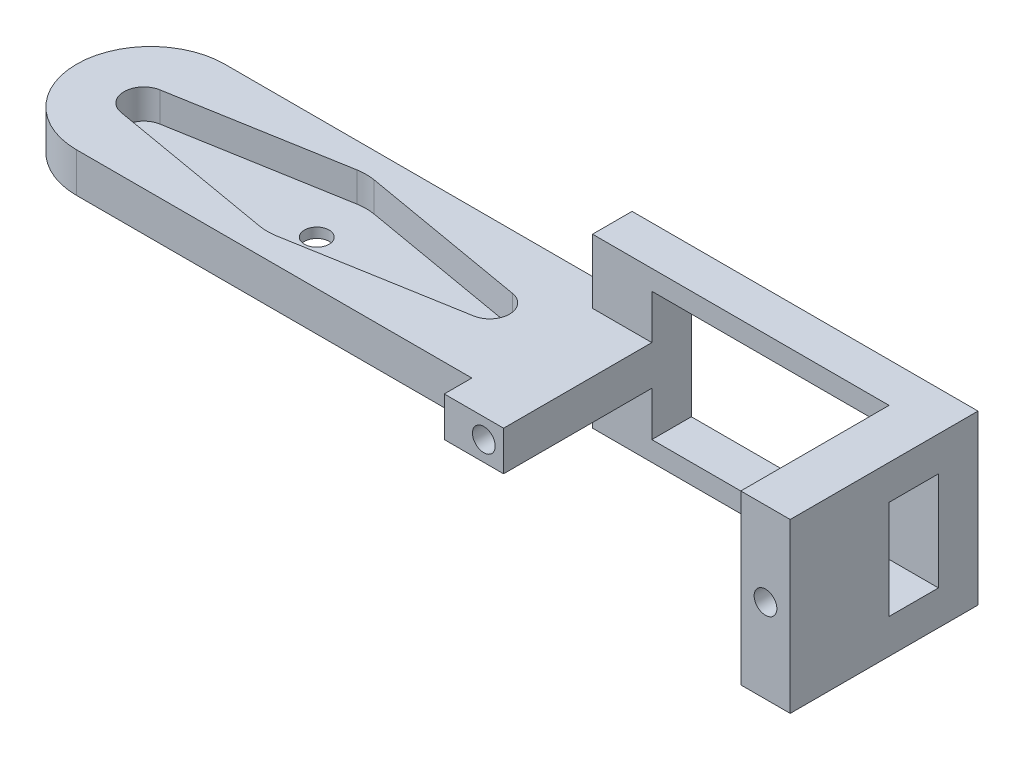
SolidWorks part; units mm, degrees
ref_plane "前基準面" through (0, 0, 0) normal (0, 0, 1) x (1, 0, 0)
ref_plane "上基準面" through (0, 0, 0) normal (0, 1, 0) x (1, 0, 0)
ref_plane "右基準面" through (0, 0, 0) normal (1, 0, 0) x (0, 0, -1)
sketch "草圖1" plane through (0, 0, 0) normal (0, 0, 1) x (1, 0, 0)
  line L0 (-21.2211, 2.8) -> (13.7789, 2.8) construction
  line L1 (-21.2211, 11.3) -> (13.7789, 11.3)
  line L2 (-21.2211, 11.3) -> (-21.2211, -5.7)
  line L3 (-21.2211, -5.7) -> (13.7789, -5.7)
  line L4 (13.7789, 11.3) -> (13.7789, -5.7)
  dimension "D1" = 35
  dimension "D2" = 8.5
extrude "填料-伸長1" add sketch "草圖1" along normal blind 4
sketch "草圖2" plane through (0, 0, 0) normal (0, 0, 1) x (1, 0, 0)
  line L0 (-21.2211, 2.8) -> (13.7789, 2.8) construction
  line L1 (-21.2211, 11.3) -> (-21.2211, -5.7) construction
  line L2 (13.7789, -5.7) -> (13.7789, 11.3) construction
  line L3 (-3.7211, 11.3) -> (-3.7211, -5.7) construction
  line L4 (13.7789, 11.3) -> (-21.2211, 11.3) construction
  line L5 (-21.2211, -5.7) -> (13.7789, -5.7) construction
  line L7 (-15.2211, 9.3) -> (8.7789, 9.3)
  line L8 (-15.2211, 9.3) -> (-15.2211, -3.7)
  line L9 (-15.2211, -3.7) -> (8.7789, -3.7)
  line L10 (8.7789, 9.3) -> (8.7789, -3.7)
  dimension "D1" = 24
  dimension "D2" = 13
  dimension "D3" = 6.5
  dimension "D4" = 5
extrude "除料-伸長1" cut sketch "草圖2" along normal blind 6
ref_plane "平面1" through (13.7789, 0, 0) normal (1, 0, 0) x (0, 0, -1)
sketch "草圖3" plane through (13.7789, 0, 0) normal (1, 0, 0) x (0, 0, -1)
  line L0 (-4, 2.8025) -> (-19, 2.8025) construction
  line L1 (-4, 11.3) -> (-19, 11.3)
  line L3 (-4, -5.6949) -> (-19, -5.6949)
  line L4 (-19, 11.3) -> (-19, -5.6949)
  line L5 (-4, 11.3) -> (-4, -5.6949)
  line L6 (-9, 7.8025) -> (-4, 7.8025)
  line L7 (-9, 7.8025) -> (-9, -2.1975)
  line L8 (-9, -2.1975) -> (-4, -2.1975)
  line L9 (-4, 7.8025) -> (-4, -2.1975)
  dimension "D1" = 15
  dimension "D2" = 5
  dimension "D3" = 10
  dimension "D4" = 5
extrude "填料-伸長2" add sketch "草圖3" against normal blind 5 contours L7 L0 L4 L3 L5 L8 | L0 L7 L6 L5 L1 L4
ref_plane "平面2" through (0, 0, 4) normal (0, 0, 1) x (1, 0, 0)
sketch "草圖5" plane through (0, 0, 4) normal (0, 0, 1) x (1, 0, 0)
  line L0 (-21.2211, 2.8) -> (-15.2211, 2.8) construction
  line L1 (-21.2211, 11.3) -> (-21.2211, -5.7) construction
  line L2 (-15.2211, -3.7) -> (-15.2211, 9.3) construction
  line L3 (-17.2211, 4.8) -> (-17.2211, 0.8) construction
  line L4 (-19.2211, 4.8) -> (-15.2211, 4.8)
  line L5 (-19.2211, 4.8) -> (-19.2211, 0.8)
  line L6 (-19.2211, 0.8) -> (-15.2211, 0.8)
  line L7 (-15.2211, 4.8) -> (-15.2211, 0.8)
  circle A0 centre (-17.2211, 2.8) radius 1.15
  dimension "D4" = 2.3
  dimension "D1" = 4
  dimension "D2" = 4
  dimension "D3" = 2
extrude "填料-伸長3" add sketch "草圖5" along normal blind 15
ref_plane "平面3" through (0, 0, 19) normal (0, 0, 1) x (1, 0, 0)
sketch "草圖6" plane through (0, 0, 19) normal (0, 0, 1) x (1, 0, 0)
  line L0 (8.7789, 2.8025) -> (13.7789, 2.8025) construction
  line L1 (8.7789, 11.3) -> (8.7789, -5.6949) construction
  line L2 (13.7789, -9.35) -> (13.7789, 9.35) construction
  line L3 (11.2789, 11.3) -> (11.2789, -5.6949) construction
  line L4 (8.7789, 11.3) -> (13.7789, 11.3) construction
  line L5 (8.7789, -5.6949) -> (13.7789, -5.6949) construction
  circle A0 centre (11.2789, 2.8025) radius 1.15
  dimension "D1" = 2.3
extrude "除料-伸長2" cut sketch "草圖6" against normal blind 15
ref_plane "平面4" through (-21.2211, 0, 0) normal (-1, 0, 0) x (0, 0, 1)
sketch "草圖7" plane through (-21.2211, 0, 0) normal (-1, 0, 0) x (0, 0, 1)
  line L6 (4, 4.8) -> (4, 0.7965)
  line L7 (4, -9.35) -> (4, 9.35) construction
  line L8 (19, 4.8) -> (4, 4.8) construction
  line L9 (4, 0.7965) -> (19, 0.8)
  line L10 (19, -2.75) -> (19, 2.75) construction
  line L11 (19, 0.8) -> (4, 0.8) construction
  line L12 (19, 0.8) -> (19, 4.8)
  line L13 (19, 4.8) -> (4, 4.8)
extrude "填料-伸長5" add sketch "草圖7" against normal blind 2
ref_plane "平面5" through (0, 0.8, 0) normal (0, -1, 0) x (-1, 0, 0)
sketch "草圖9" plane through (0, 0.8, 0) normal (0, -1, 0) x (-1, 0, 0)
  line L0 (21.2211, -1.2098) -> (21.2211, -16.2098)
  line L1 (21.2211, -4) -> (21.2211, 0) construction
  line L2 (21.2211, -4) -> (21.2211, -19) construction
  line L3 (21.2211, -16.2098) -> (61.2211, -16.2098)
  line L4 (21.2211, -1.2098) -> (61.2211, -1.2098)
  arc A0 (61.2211, -1.2098) -> (61.2211, -16.2098) centre (61.2211, -8.7098) cw
  dimension "D1" = 15
  dimension "D2" = 40
  dimension "D3" = 40
extrude "填料-伸長6" add sketch "草圖9" against normal blind 4
ref_plane "平面6" through (0, 4.8, 0) normal (0, 1, 0) x (1, 0, 0)
sketch "草圖10" plane through (0, 4.8, 0) normal (0, 1, 0) x (1, 0, 0)
  line L4 (-68.7211, -8.7098) -> (-59.9107, -8.7098) construction
  line L5 (-45.2679, -3.7838) -> (-62.2536, -6.7394)
  line L6 (-44.4107, -13.7098) -> (-44.4107, -16.2098) construction
  line L7 (-21.2211, -16.2098) -> (-61.2211, -16.2098) construction
  line L8 (-45.2679, -13.6358) -> (-62.2536, -10.6802)
  line L9 (-43.5536, -13.6358) -> (-26.5679, -10.6802)
  line L10 (-43.5536, -3.7838) -> (-26.5679, -6.7394)
  line L11 (-24.9107, -8.7098) -> (-20.1004, -8.7098) construction
  arc A2 (-61.2211, -1.2098) -> (-61.2211, -16.2098) centre (-61.2211, -8.7098) ccw construction
  arc A3 (-45.2679, -13.6358) -> (-43.5536, -13.6358) centre (-44.4107, -8.7098) ccw
  arc A4 (-62.2536, -6.7394) -> (-62.2536, -10.6802) centre (-61.9107, -8.7098) ccw
  arc A5 (-26.5679, -10.6802) -> (-26.5679, -6.7394) centre (-26.9107, -8.7098) ccw
  arc A6 (-43.5536, -3.7838) -> (-45.2679, -3.7838) centre (-44.4107, -8.7098) ccw
  dimension "D1" = 10
  dimension "D5" = 4
  dimension "D2" = 17.5
  dimension "D3" = 17.5
extrude "除料-伸長3" cut sketch "草圖10" against normal blind 3
sketch "草圖11" plane through (0, 4.8, 0) normal (0, 1, 0) x (1, 0, 0)
  line L0 (-63.9107, -8.7098) -> (-24.9107, -8.7098) construction
  line L1 (-44.4107, -3.7098) -> (-44.4107, -13.7098) construction
  arc A0 (-62.2536, -6.7394) -> (-62.2536, -10.6802) centre (-61.9107, -8.7098) ccw construction
  arc A1 (-26.5679, -10.6802) -> (-26.5679, -6.7394) centre (-26.9107, -8.7098) ccw construction
  arc A2 (-43.5536, -3.7838) -> (-45.2679, -3.7838) centre (-44.4107, -8.7098) ccw construction
  arc A3 (-45.2679, -13.6358) -> (-43.5536, -13.6358) centre (-44.4107, -8.7098) ccw construction
  circle A4 centre (-44.4107, -8.7098) radius 1.25
  dimension "D1" = 2.5
extrude "除料-伸長4" cut sketch "草圖11" against normal blind 13.4
